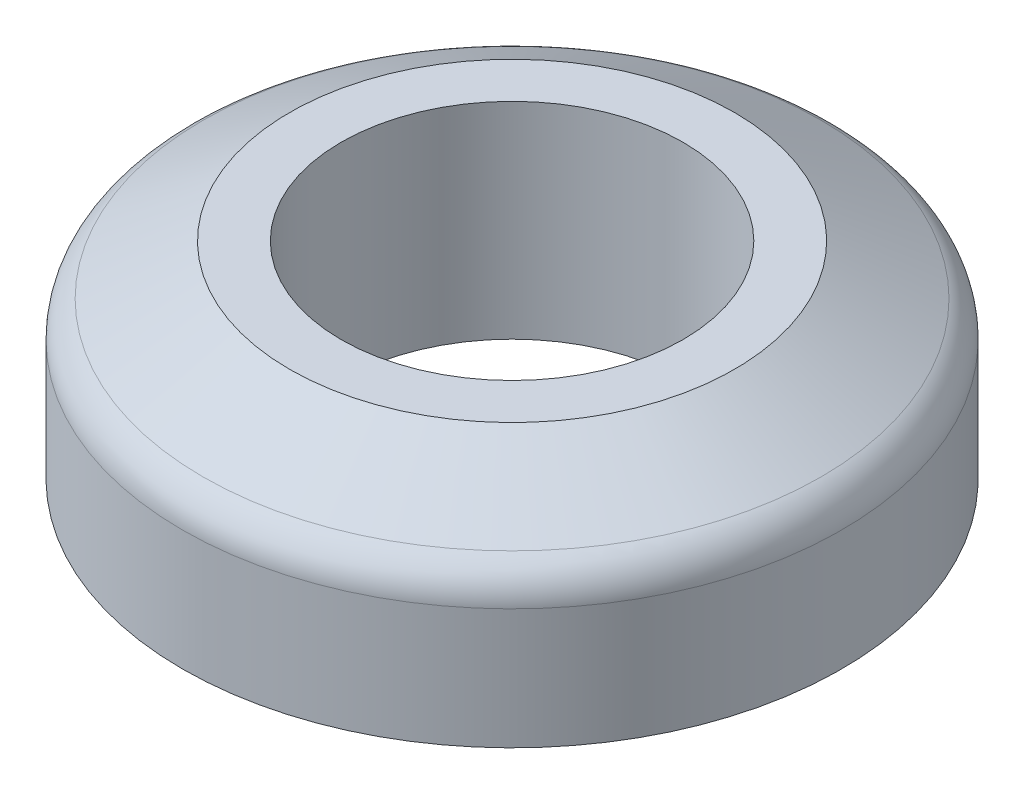
SolidWorks part; units mm, degrees
ref_plane "Front Plane" through (0, 0, 0) normal (0, 0, 1) x (1, 0, 0)
ref_plane "Top Plane" through (0, 0, 0) normal (0, 1, 0) x (1, 0, 0)
ref_plane "Right Plane" through (0, 0, 0) normal (1, 0, 0) x (0, 0, -1)
sketch "Sketch1" plane through (0, 0, 0) normal (0, 1, 0) x (1, 0, 0)
  circle A0 centre (0, 0) radius 4.15
  circle A1 centre (0, 0) radius 8
  dimension "D1" = 8.3
  dimension "D2" = 16
extrude "Boss-Extrude1" add sketch "Sketch1" along normal blind 5
chamfer "Chamfer1" distance 2.6 angle 30 1 edges at (0, 5, 8)
fillet "Fillet1" radius 1 1 edges at (0, 3.4989, 8)
